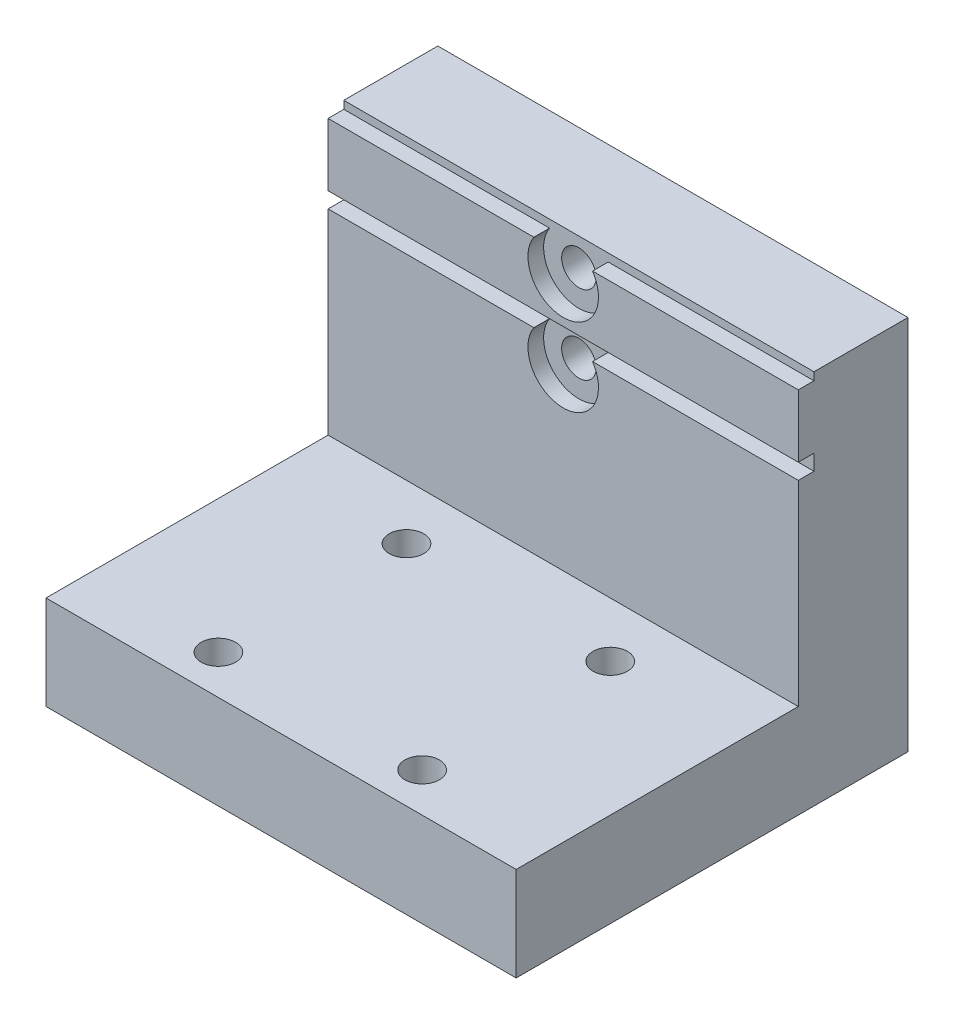
SolidWorks part; units mm, degrees
ref_plane "Plano frontal" through (0, 0, 0) normal (0, 0, 1) x (1, 0, 0)
ref_plane "Plano superior" through (0, 0, 0) normal (0, 1, 0) x (1, 0, 0)
ref_plane "Plano direito" through (0, 0, 0) normal (1, 0, 0) x (0, 0, -1)
sketch "Esboço1" plane through (0, 0, 0) normal (1, 0, 0) x (0, 0, -1)
  line L0 (0, 0) -> (0, -18)
  line L2 (7, -24) -> (7, 0)
  line L3 (7, 0) -> (0, 0)
  line L4 (0, -18) -> (-18, -18)
  line L5 (-18, -18) -> (-18, -24)
  line L6 (-18, -24) -> (7, -24)
  dimension "D1" = 18
  dimension "D2" = 7
  dimension "D3" = 6
  dimension "D4" = 18
extrude "Ressalto-extrusão1" add sketch "Esboço1" along normal mid plane 30
sketch "Esboço3" plane through (0, -18, 0) normal (0, -1, 0) x (1, 0, 0)
  line L0 (2.4577, 9.5) -> (-2.4577, 9.5) construction
  line L1 (0, 18) -> (0, 9.5) construction
  line L9 (15, 18) -> (-15, 18) construction
  circle A0 centre (-6.5, 15.5) radius 1.1
  circle A1 centre (6.5, 15.5) radius 1.1
  circle A2 centre (6.5, 3.5) radius 1.1
  circle A3 centre (-6.5, 3.5) radius 1.1
  dimension "D3" = 2.2
  dimension "D1" = 12
  dimension "D2" = 13
  dimension "D4" = 9.5
extrude "Corte-extrusão1" cut sketch "Esboço3" along normal blind 30
sketch "Esboço15" plane through (0, 0, 0) normal (0, 0, 1) x (1, 0, 0)
  line L0 (-1.8708, -4.5) -> (-15, -4.5)
  line L1 (15, 0) -> (15, -18) construction
  line L2 (15, -5.5) -> (1.8708, -5.5)
  line L3 (15, -5.5) -> (15, -4.5)
  line L4 (15, -4.5) -> (1.8708, -4.5)
  line L5 (-15, -5.5) -> (-15, -4.5)
  line L6 (-15, 0) -> (-15, -18) construction
  line L7 (-1.8708, -5.5) -> (1.8708, -5.5) construction
  line L8 (15, -0.5) -> (1.8708, -0.5)
  line L9 (15, -0.5) -> (15, 0.5)
  line L10 (15, 0.5) -> (1.8708, 0.5)
  line L11 (-15, -0.5) -> (-15, 0.5)
  line L12 (15, -2.5) -> (-15, -2.5) construction
  line L13 (1.8708, -4.5) -> (-1.8708, -4.5)
  line L14 (1.8708, 0.5) -> (-1.8708, 0.5)
  line L15 (15, 0) -> (-15, 0) construction
  line L16 (0, -2.5) -> (0, -11.2094) construction
  line L17 (0, -2.5) -> (14.855, -2.5) construction
  line L18 (-1.8708, 0.5) -> (-15, 0.5)
  line L19 (-1.8708, -5.5) -> (-15, -5.5)
  line L20 (-1.8708, -0.5) -> (-15, -0.5)
  arc A0 (-1.8708, -5.5) -> (1.8708, -5.5) centre (0, -6.75) ccw
  circle A2 centre (0, -6.75) radius 1.1 construction
  arc A3 (1.8708, 0.5) -> (-1.8708, 0.5) centre (0, 1.75) ccw construction
  arc A4 (1.8708, -4.5) -> (-1.8708, -4.5) centre (0, -3.25) ccw construction
  arc A5 (-1.8708, -0.5) -> (1.8708, -0.5) centre (0, -1.75) ccw
  point P16 (15, 0)
  point P17 (15, -5)
  point P33 (0, 0)
  point P36 (-1.6246, -5.3)
  dimension "D4" = 2.2
  dimension "D5" = 4.5
  dimension "D1" = 2.5
  dimension "D2" = 5
  dimension "D3" = 1
extrude "Corte-extrusão8" cut sketch "Esboço15" against normal blind 1
sketch "Esboço16" plane through (0, 0, 0) normal (0, 0, 1) x (1, 0, 0)
  circle A0 centre (0, -1.75) radius 1.1
  circle A1 centre (0, -6.75) radius 1.1
  arc A3 (-1.8708, -5.5) -> (1.8708, -5.5) centre (0, -6.75) ccw construction
  arc A4 (-1.8708, -0.5) -> (1.8708, -0.5) centre (0, -1.75) ccw construction
  dimension "D1" = 2.2
extrude "Corte-extrusão9" cut sketch "Esboço16" against normal up to surface (7 mm away) up to face at (0, -12, -7)
sketch "Esboço17" plane through (0, 0, -7) normal (0, 0, -1) x (-1, 0, 0)
  circle A0 centre (0, -1.75) radius 1.6
  circle A1 centre (0, -6.75) radius 1.6
  dimension "D1" = 3.2
extrude "Corte-extrusão10" cut sketch "Esboço17" against normal offset from surface (3 mm away) 3 from surface at 0 up to face at (1.1, -1.75, -7) starting at face at (1.1, -1.75, -7)
sketch "Esboço18" plane through (0, 0, -7) normal (0, 0, -1) x (-1, 0, 0)
  line L0 (-15, -24) -> (15, -24) construction
  line L1 (0, -24) -> (0, -14.7064) construction
  circle A0 centre (12.5, -21) radius 1.6
  circle A1 centre (-12.5, -21) radius 1.6
  dimension "D2" = 3.2
  dimension "D1" = 3
  dimension "D3" = 25
extrude "Corte-extrusão11" cut sketch "Esboço18" against normal blind 15
sketch "Esboço19" plane through (0, 0, -7) normal (0, 0, -1) x (-1, 0, 0)
  line L0 (0, -24) -> (0, -16.7647) construction
  line L1 (-15, -24) -> (15, -24) construction
  circle A0 centre (12.5, -21) radius 2.075
  circle A1 centre (-12.5, -21) radius 2.075
  dimension "D1" = 4.15
extrude "Corte-extrusão12" cut sketch "Esboço19" against normal blind 4
sketch "Esboço20" plane through (0, -24, 0) normal (0, -1, 0) x (1, 0, 0)
  circle A0 centre (-6.5, 15.5) radius 2.2
  circle A1 centre (6.5, 15.5) radius 2.2
  circle A2 centre (6.5, 3.5) radius 2.2
  circle A3 centre (-6.5, 3.5) radius 2.2
  dimension "D1" = 4.4
extrude "Corte-extrusão13" cut sketch "Esboço20" against normal blind 2
